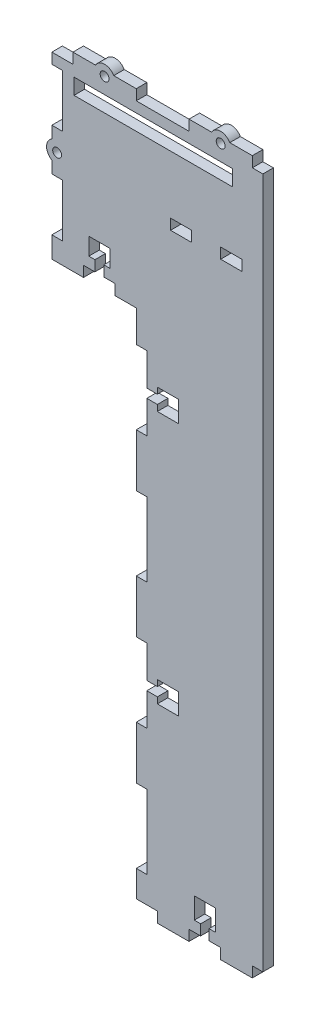
SolidWorks part; units mm, degrees
ref_plane "Front Plane" through (0, 0, 0) normal (0, 0, 1) x (1, 0, 0)
ref_plane "Top Plane" through (0, 0, 0) normal (0, 1, 0) x (1, 0, 0)
ref_plane "Right Plane" through (0, 0, 0) normal (1, 0, 0) x (0, 0, -1)
sketch "Sketch1" plane through (0, 0, 0) normal (0, 0, 1) x (1, 0, 0)
  line L1 (0, 0) -> (-106, 0)
  line L2 (0, 0) -> (0, 327.5)
  line L3 (0, 327.5) -> (-106, 327.5)
  line L4 (-106, 0) -> (-106, 327.5)
  dimension "D1" = 106
  dimension "D2" = 327.5
extrude "Boss-Extrude1" add sketch "Sketch1" along normal blind 5
sketch "Sketch2" plane through (0, 0, 5) normal (0, 0, 1) x (1, 0, 0)
  line L1 (-106, 0) -> (-66, 0)
  line L2 (-106, 0) -> (-106, 242.5)
  line L3 (-106, 242.5) -> (-66, 242.5)
  line L4 (-66, 0) -> (-66, 242.5)
  dimension "D1" = 242.5
  dimension "D2" = 40
extrude "Cut-Extrude1" cut sketch "Sketch2" against normal blind 5
sketch "Sketch3" plane through (0, 0, 5) normal (0, 0, 1) x (1, 0, 0)
  line L0 (-106, 327.5) -> (-106, 242.5) construction
  line L1 (-101, 297.5) -> (-106, 297.5)
  line L2 (-101, 297.5) -> (-101, 322.5)
  line L3 (-101, 322.5) -> (-106, 322.5)
  line L4 (-106, 297.5) -> (-106, 322.5)
  line L5 (0, 327.5) -> (-106, 327.5) construction
  line L7 (-106, 277.5) -> (-101, 277.5)
  line L8 (-106, 277.5) -> (-106, 252.5)
  line L9 (-106, 252.5) -> (-101, 252.5)
  line L10 (-101, 277.5) -> (-101, 252.5)
  dimension "D1" = 25
  dimension "D2" = 5
  dimension "D3" = 5
  dimension "D4" = 5
  dimension "D5" = 25
  dimension "D6" = 20
extrude "Cut-Extrude2" cut sketch "Sketch3" against normal blind 5
sketch "Sketch4" plane through (0, 0, 5) normal (0, 0, 1) x (1, 0, 0)
  line L0 (0, 327.5) -> (-106, 327.5) construction
  line L1 (-41, 327.5) -> (-11, 327.5)
  line L2 (-41, 327.5) -> (-41, 332.5)
  line L3 (-41, 332.5) -> (-11, 332.5)
  line L4 (-11, 327.5) -> (-11, 332.5)
  line L6 (-53.5, 327.5) -> (-53.5, 320.952) construction
  line L7 (-96, 327.5) -> (-96, 332.5)
  line L8 (-66, 332.5) -> (-96, 332.5)
  line L9 (-66, 327.5) -> (-66, 332.5)
  line L10 (-66, 327.5) -> (-96, 327.5)
  line L11 (0, 0) -> (0, 327.5) construction
  dimension "D1" = 30
  dimension "D2" = 53.5
  dimension "D3" = 5
  dimension "D4" = 12.5
extrude "Boss-Extrude2" add sketch "Sketch4" against normal blind 5
sketch "Sketch5" plane through (0, 0, 5) normal (0, 0, 1) x (1, 0, 0)
  line L0 (-66, 242.5) -> (-106, 242.5) construction
  line L1 (-76, 242.5) -> (-91, 242.5)
  line L2 (-76, 242.5) -> (-76, 247.5)
  line L3 (-76, 247.5) -> (-91, 247.5)
  line L4 (-91, 242.5) -> (-91, 247.5)
  line L5 (-106, 252.5) -> (-106, 242.5) construction
  dimension "D1" = 15
  dimension "D2" = 5
  dimension "D3" = 15
extrude "Cut-Extrude3" cut sketch "Sketch5" against normal blind 5
sketch "Sketch6" plane through (0, 0, 5) normal (0, 0, 1) x (1, 0, 0)
  line L0 (-66, 0) -> (-66, 242.5) construction
  line L1 (-66, 242.5) -> (-61, 242.5)
  line L2 (-66, 242.5) -> (-66, 227.5)
  line L3 (-66, 227.5) -> (-61, 227.5)
  line L4 (-61, 242.5) -> (-61, 227.5)
  line L5 (-66, 192.5) -> (-61, 192.5)
  line L6 (-66, 192.5) -> (-66, 167.5)
  line L7 (-66, 167.5) -> (-61, 167.5)
  line L8 (-61, 192.5) -> (-61, 167.5)
  line L9 (-61, 227.5) -> (-61, 192.5)
  line L10 (-66, 132.5) -> (-61, 132.5)
  line L11 (-66, 132.5) -> (-66, 107.5)
  line L12 (-66, 107.5) -> (-61, 107.5)
  line L13 (-61, 132.5) -> (-61, 107.5)
  line L14 (-66, 72.5) -> (-61, 72.5)
  line L15 (-66, 72.5) -> (-66, 47.5)
  line L16 (-66, 47.5) -> (-61, 47.5)
  line L17 (-61, 72.5) -> (-61, 47.5)
  line L18 (-66, 0) -> (-61, 0)
  line L19 (-66, 0) -> (-66, 12.5)
  line L20 (-66, 12.5) -> (-61, 12.5)
  line L21 (-61, 0) -> (-61, 12.5)
  line L22 (-61, 167.5) -> (-61, 132.5)
  line L23 (-61, 107.5) -> (-61, 72.5)
  line L24 (-61, 47.5) -> (-61, 12.5)
  line L25 (-66, 12.5) -> (-66, 47.5)
  line L26 (-66, 72.5) -> (-66, 107.5)
  line L27 (-66, 132.5) -> (-66, 167.5)
  line L28 (-66, 227.5) -> (-66, 192.5)
  line M17 (-66, 242.5) -> (-66, 0)
  dimension "D1" = 15
  dimension "D2" = 5
  dimension "D3" = 25
  dimension "D4" = 35
  dimension "D5" = 5
  dimension "D6" = 25
  dimension "D7" = 35
  dimension "D8" = 5
  dimension "D9" = 25
  dimension "D10" = 35
  dimension "D11" = 5
  dimension "D12" = 5
  dimension "D13" = 12.5
extrude "Cut-Extrude4" cut sketch "Sketch6" against normal blind 5 contours L9 L3 L5 M17 | L22 L7 L10 M17 | L23 L12 L14 M17 | L24 L16 L20 M17
sketch "Sketch7" plane through (0, 0, 5) normal (0, 0, 1) x (1, 0, 0)
  line L0 (-11, 332.5) -> (-41, 332.5) construction
  line L1 (-26, 287.5) -> (-16, 287.5)
  line L2 (-26, 287.5) -> (-26, 282.5)
  line L3 (-26, 282.5) -> (-16, 282.5)
  line L4 (-16, 287.5) -> (-16, 282.5)
  line L5 (0, 0) -> (0, 327.5) construction
  line L7 (-39.75, 282.5) -> (-49.75, 282.5)
  line L8 (-39.75, 282.5) -> (-39.75, 287.5)
  line L9 (-39.75, 287.5) -> (-49.75, 287.5)
  line L10 (-49.75, 282.5) -> (-49.75, 287.5)
  dimension "D1" = 45
  dimension "D2" = 16
  dimension "D3" = 10
  dimension "D4" = 5
  dimension "D5" = 5
  dimension "D6" = 10
  dimension "D7" = 13.75
extrude "Cut-Extrude5" cut sketch "Sketch7" against normal blind 5
sketch "Sketch8" plane through (0, 0, 5) normal (0, 0, 1) x (1, 0, 0)
  line L0 (-66, 0) -> (0, 0) construction
  line L1 (-26, 0) -> (-11, 0)
  line L2 (-26, 0) -> (-26, -5)
  line L3 (-26, -5) -> (-11, -5)
  line L4 (-11, 0) -> (-11, -5)
  line L6 (-56, 0) -> (-41, 0)
  line L7 (-56, 0) -> (-56, -5)
  line L8 (-56, -5) -> (-41, -5)
  line L9 (-41, 0) -> (-41, -5)
  point P6 (-11, -2.5)
  dimension "D1" = 5
  dimension "D2" = 11
  dimension "D3" = 15
  dimension "D4" = 15
  dimension "D5" = 5
  dimension "D6" = 15
extrude "Boss-Extrude3" add sketch "Sketch8" against normal blind 5
sketch "Sketch9" plane through (0, 0, 0) normal (0, 0, -1) x (-1, 0, 0)
  line L0 (11, 332.5) -> (41, 332.5) construction
  line L1 (20.5, 322.5) -> (90.5, 322.5)
  line L2 (20.5, 322.5) -> (20.5, 315)
  line L3 (20.5, 315) -> (90.5, 315)
  line L4 (90.5, 322.5) -> (90.5, 315)
  line L5 (0, 0) -> (0, 327.5) construction
  dimension "D1" = 7.5
  dimension "D2" = 10
  dimension "D3" = 70
  dimension "D4" = 20.5
extrude "Cut-Extrude6" cut sketch "Sketch9" against normal blind 5
sketch "Sketch10" plane through (0, 0, 0) normal (0, 0, -1) x (-1, 0, 0)
  line L0 (0, 0) -> (0, 327.5) construction
  line L1 (0, 277.5) -> (-5, 277.5)
  line L2 (0, 277.5) -> (0, 50)
  line L3 (0, 50) -> (-5, 50)
  line L4 (-5, 277.5) -> (-5, 50)
  line L5 (26, -5) -> (11, -5) construction
  line L6 (0, 327.5) -> (11, 327.5) construction
  dimension "D1" = 5
  dimension "D2" = 55
  dimension "D3" = 50
extrude "Boss-Extrude4" add sketch "Sketch10" against normal blind 5
sketch "Sketch11" plane through (0, 0, 0) normal (0, 0, -1) x (-1, 0, 0)
  line L0 (-5, 50) -> (0, 50) construction
  line L1 (-5, 277.5) -> (-5, 50) construction
  line L2 (-5, 163.75) -> (14.968, 163.75) construction
  circle A0 centre (-2.5, 75) radius 2.1
  circle A1 centre (-2.5, 252.5) radius 2.1
  dimension "D1" = 4.2
  dimension "D2" = 25
  dimension "D3" = 2.5
extrude "Cut-Extrude7" cut sketch "Sketch11" against normal blind 5
sketch "Sketch12" plane through (0, 0, 0) normal (0, 0, -1) x (-1, 0, 0)
  line L0 (-5, 277.5) -> (-5, 50) construction
  line L1 (-5, 70.6699) -> (-5, 79.3301)
  line L2 (-5, 163.75) -> (15.7992, 163.75) construction
  line L3 (-5, 256.8301) -> (-5, 248.1699)
  arc A0 (-5, 79.3301) -> (-5, 70.6699) centre (-2.5, 75) ccw
  arc A1 (-5, 248.1699) -> (-5, 256.8301) centre (-2.5, 252.5) cw
  dimension "D1" = 5
extrude "Boss-Extrude5" add sketch "Sketch12" against normal blind 5
sketch "Sketch13" plane through (0, 0, 0) normal (0, 0, -1) x (-1, 0, 0)
  line L0 (0, 327.5) -> (11, 327.5) construction
  line L1 (-5, 0) -> (5, 0)
  line L2 (-5, 0) -> (-5, 327.5)
  line L3 (-5, 327.5) -> (5, 327.5)
  line L4 (5, 0) -> (5, 327.5)
  line L5 (0, 277.5) -> (0, 327.5) construction
  line L7 (-16.1184, 267.8097) -> (-5, 267.8097)
  line L8 (-16.1184, 267.8097) -> (-16.1184, 236.5439)
  line L9 (-16.1184, 236.5439) -> (-5, 236.5439)
  line L10 (-5, 267.8097) -> (-5, 236.5439)
  line L11 (-29.9931, 97.023) -> (-5, 97.023)
  line L12 (-29.9931, 97.023) -> (-29.9931, 60.9929)
  line L13 (-29.9931, 60.9929) -> (-5, 60.9929)
  line L14 (-5, 97.023) -> (-5, 60.9929)
  point P6 (0, 327.5)
  dimension "D1" = 10
extrude "Cut-Extrude8" cut sketch "Sketch13" against normal blind 10 contours L1 L4 L3 L2 | L8 L9 L2 L7 | L12 L13 L2 L11
sketch "Sketch14" plane through (-5, 0, 0) normal (1, 0, 0) x (0, 0, -1)
  line L4 (-5, 327.5) -> (-5, 0)
  line L5 (-5, 0) -> (0, 0)
  line L6 (0, 0) -> (0, 327.5)
  line L7 (0, 327.5) -> (-5, 327.5)
  line L8 (-5, 327.5) -> (-5, 0)
  line L9 (-5, 0) -> (0, 0)
  line L10 (0, 0) -> (0, 327.5)
  line L11 (0, 327.5) -> (-5, 327.5)
  dimension "D1" = 0
extrude "Cut-Extrude9" cut sketch "Sketch14" against normal blind 1
sketch "Sketch15" plane through (0, 0, 0) normal (0, 0, -1) x (-1, 0, 0)
  line L0 (76, 247.5) -> (91, 247.5) construction
  line L1 (81.4, 247.5) -> (85.6, 247.5)
  line L2 (81.4, 247.5) -> (81.4, 252.5)
  line L3 (81.4, 252.5) -> (85.6, 252.5)
  line L4 (85.6, 247.5) -> (85.6, 252.5)
  line L5 (61, 210) -> (45.21, 210) construction
  line L6 (78.5, 260.7) -> (88.5, 260.7)
  line L7 (78.5, 260.7) -> (78.5, 252.5)
  line L8 (78.5, 252.5) -> (88.5, 252.5)
  line L9 (88.5, 260.7) -> (88.5, 252.5)
  line L10 (61, 227.5) -> (61, 192.5) construction
  line L11 (61, 150) -> (35.4087, 150) construction
  line L12 (61, 212.1) -> (56, 212.1)
  line L13 (61, 212.1) -> (61, 207.9)
  line L14 (61, 207.9) -> (56, 207.9)
  line L15 (56, 212.1) -> (56, 207.9)
  line L16 (56, 205) -> (46, 205)
  line L17 (56, 205) -> (56, 215)
  line L18 (56, 215) -> (46, 215)
  line L19 (46, 205) -> (46, 215)
  line L20 (61, 167.5) -> (61, 132.5) construction
  line L21 (61, 90) -> (45.21, 90) construction
  line L22 (46, 95) -> (46, 85)
  line L23 (56, 85) -> (46, 85)
  line L24 (56, 95) -> (56, 85)
  line L25 (56, 95) -> (46, 95)
  line L26 (56, 87.9) -> (56, 92.1)
  line L27 (61, 92.1) -> (56, 92.1)
  line L28 (61, 87.9) -> (61, 92.1)
  line L29 (61, 87.9) -> (56, 87.9)
  point P10 (83.5, 260.7)
  point P11 (83.5, 252.5)
  point P12 (83.5, 247.5)
  point P13 (83.5, 247.5)
  point P26 (56, 210)
  point P27 (46, 210)
  point P28 (56, 210)
  dimension "D1" = 5
  dimension "D2" = 4.2
  dimension "D3" = 10
  dimension "D4" = 8.2
  dimension "D5" = 4.2
  dimension "D6" = 10
  dimension "D7" = 5
  dimension "D8" = 10
extrude "Cut-Extrude10" cut sketch "Sketch15" against normal blind 10 contours L9 L6 L7 L8 L3 | L1 L4 L3 L2 | L19 L16 L17 L15 L18 | L12 L15 L14 L13 | L24 L25 L22 L23 | L29 L28 L27 L24
sketch "Sketch16" plane through (0, 0, 0) normal (0, 0, -1) x (-1, 0, 0)
  line L0 (106, 297.5) -> (101, 297.5) construction
  line L1 (106, 297.5) -> (106, 277.5) construction
  circle A0 centre (103.5, 287.5) radius 2.1
  dimension "D1" = 4.2
  dimension "D2" = 10
  dimension "D3" = 2.5
extrude "Cut-Extrude11" cut sketch "Sketch16" against normal blind 10
sketch "Sketch17" plane through (0, 0, 0) normal (0, 0, -1) x (-1, 0, 0)
  line L0 (106, 297.5) -> (106, 277.5) construction
  line L1 (106, 283.1699) -> (106, 291.8301)
  arc A0 (106, 291.8301) -> (106, 283.1699) centre (103.5, 287.5) cw
  dimension "D1" = 5
extrude "Boss-Extrude6" add sketch "Sketch17" against normal blind 5
sketch "Sketch18" plane through (0, 0, 0) normal (0, 0, -1) x (-1, 0, 0)
  line L0 (41, 0) -> (26, 0) construction
  line L1 (31.4, 0) -> (35.6, 0)
  line L2 (31.4, 0) -> (31.4, 5)
  line L3 (31.4, 5) -> (35.6, 5)
  line L4 (35.6, 0) -> (35.6, 5)
  line L6 (28.5, 5) -> (38.5, 5)
  line L7 (28.5, 5) -> (28.5, 13.2)
  line L8 (28.5, 13.2) -> (38.5, 13.2)
  line L9 (38.5, 5) -> (38.5, 13.2)
  point P10 (33.5, 0)
  point P11 (33.5, 13.2)
  point P12 (33.5, 0)
  dimension "D1" = 10
  dimension "D2" = 8.2
  dimension "D3" = 5
  dimension "D4" = 4.2
extrude "Cut-Extrude12" [suppressed] cut sketch "Sketch18" against normal blind 5 contours L6 L9 L8 L7 L3 | L1 L4 L3 L2
sketch "Sketch19" plane through (0, 0, 5) normal (0, 0, 1) x (1, 0, 0)
  line L0 (-41, 0) -> (-26, 0) construction
  line L1 (-35.5, 0) -> (-31.5, 0)
  line L2 (-35.5, 0) -> (-35.5, 5)
  line L3 (-35.5, 5) -> (-31.5, 5)
  line L4 (-31.5, 0) -> (-31.5, 5)
  line L6 (-38.5, 15) -> (-28.5, 15)
  line L7 (-38.5, 15) -> (-38.5, 5)
  line L8 (-38.5, 5) -> (-28.5, 5)
  line L9 (-28.5, 15) -> (-28.5, 5)
  point P10 (-33.5, 15)
  point P11 (-33.5, 5)
  point P12 (-33.5, 0)
  dimension "D1" = 4
  dimension "D2" = 10
  dimension "D3" = 10
  dimension "D4" = 5
  dimension "D5" = 5
extrude "Cut-Extrude13" cut sketch "Sketch19" against normal blind 5 contours L8 L2 L1 L4 | L2 L8 L4 L6 | L2 L6 L4 L3 | L9 L6 L4 L8 | L7 L8 L2 L6
sketch "Sketch20" plane through (0, 0, 0) normal (0, 0, -1) x (-1, 0, 0)
  line L0 (41, 332.5) -> (41, 327.5) construction
  line L1 (41, 327.5) -> (66, 327.5) construction
  line L2 (53.5, 327.5) -> (53.5, 323.9665) construction
  circle A0 centre (26, 330) radius 2.1
  circle A1 centre (81, 330) radius 2.1
  dimension "D1" = 4.2
  dimension "D2" = 15
  dimension "D3" = 2.5
extrude "Cut-Extrude14" cut sketch "Sketch20" against normal blind 5
sketch "Sketch21" plane through (0, 0, 0) normal (0, 0, -1) x (-1, 0, 0)
  line L0 (11, 332.5) -> (41, 332.5) construction
  line L1 (30.3301, 332.5) -> (21.6699, 332.5)
  line L2 (53.5, 327.5) -> (53.5, 324.4022) construction
  line L3 (41, 327.5) -> (66, 327.5) construction
  line L4 (76.6699, 332.5) -> (85.3301, 332.5)
  arc A0 (21.6699, 332.5) -> (30.3301, 332.5) centre (26, 330) cw
  arc A1 (85.3301, 332.5) -> (76.6699, 332.5) centre (81, 330) ccw
  dimension "D1" = 5
extrude "Boss-Extrude7" add sketch "Sketch21" against normal blind 5
sketch "Sketch22" plane through (0, 0, 0) normal (0, 0, -1) x (-1, 0, 0)
  line L1 (90.5, 322.5) -> (95.5, 322.5)
  line L2 (90.5, 322.5) -> (90.5, 315)
  line L3 (90.5, 315) -> (95.5, 315)
  line L4 (95.5, 322.5) -> (95.5, 315)
  dimension "D1" = 5
  dimension "D2" = 7.5
extrude "Cut-Extrude15" cut sketch "Sketch22" against normal blind 5
